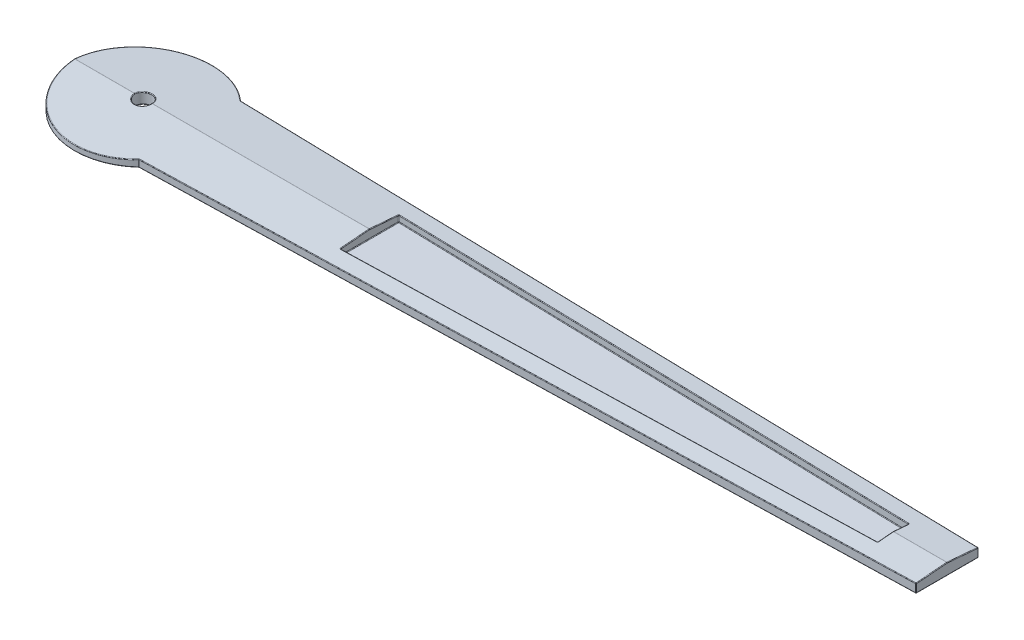
SolidWorks part; units mm, degrees
ref_plane "Front Plane" through (0, 0, 0) normal (0, 0, 1) x (1, 0, 0)
ref_plane "Top Plane" through (0, 0, 0) normal (0, 1, 0) x (1, 0, 0)
ref_plane "Right Plane" through (0, 0, 0) normal (1, 0, 0) x (0, 0, -1)
sketch "Sketch1" plane through (0, 0, 0) normal (0, 1, 0) x (1, 0, 0)
  line L0 (14.2005, 0.633) -> (0.8775, 0.8412)
  line L1 (14.2073, -0.475) -> (0.7499, -0.9567)
  line L2 (14.2005, 0.633) -> (14.2073, -0.475)
  line L3 (13.2032, 0.373) -> (13.1824, -0.2227)
  line L4 (13.1824, -0.2227) -> (3.9608, -0.5357)
  line L5 (3.9608, -0.5357) -> (3.9347, 0.4217)
  line L6 (3.9347, 0.4217) -> (13.2032, 0.373)
  arc A0 (0.8775, 0.8412) -> (0.7499, -0.9567) centre (0, 0) ccw
  circle A1 centre (0, 0) radius 0.15
sketch "Sketch2" plane through (0, 0, 0) normal (0, 1, 0) x (1, 0, 0)
  line L0 (13.25, 0.2746) -> (4, 0.5144)
  line L1 (14.2005, 0.633) -> (14.2073, -0.475) construction
  line L2 (-8.4826, 0) -> (8.4826, 0) construction
  line L3 (14.2044, 0) -> (14.2044, -0.55)
  line L4 (14.2044, 0) -> (14.2044, 0.55)
  line L7 (14.2044, 0.55) -> (0.8206, 0.8969)
  line L8 (0.8206, -0.8969) -> (14.2044, -0.55)
  line L9 (4, -0.5144) -> (13.25, -0.2746)
  line L10 (13.25, 0.2746) -> (13.25, -0.2746)
  line L13 (4, 0.5144) -> (4, -0.5144)
  line L14 (14.1966, 0.2501) -> (0.8128, 0.597) construction
  line L15 (0.8128, -0.597) -> (14.1966, -0.2501) construction
  arc A0 (0.8206, 0.8969) -> (0.8206, -0.8969) centre (0, 0) ccw
  circle A1 centre (0, 0) radius 0.15
  dimension "D1" = 0.55
  dimension "D2" = 0.55
  dimension "D3" = 0.3
  dimension "D4" = 0.3
extrude "Boss-Extrude1" add sketch "Sketch2" along normal blind 0.2
ref_plane "Plane1" through (4, 0, 0.5144) normal (0, 0, 1) x (1, 0, 0)
sketch "Sketch4" plane through (0, 0, 0) normal (0, -1, 0) x (1, 0, 0)
  line L0 (4, -0.5144) -> (4, 0.5144) construction
  line L1 (13.25, -0.2746) -> (4, -0.5144) construction
  line L2 (4, 0.5144) -> (13.25, 0.2746) construction
  line L3 (13.25, 0.2746) -> (13.25, -0.2746) construction
  line L4 (4, -0.5144) -> (4, 0.5144)
  line L5 (13.25, -0.2746) -> (4, -0.5144)
  line L6 (4, 0.5144) -> (13.25, 0.2746)
  line L7 (13.25, 0.2746) -> (13.25, -0.2746)
extrude "Boss-Extrude2" add sketch "Sketch4" against normal blind 0.05
sketch "Sketch5" plane through (0, 0, 0) normal (1, 0, 0) x (0, 0, -1)
  line L0 (-1.2156, 0.1) -> (0, 0.2)
  line L1 (-1.2156, 0.2) -> (-1.2156, 0) construction
  line L2 (-0.55, 0.2) -> (0.55, 0.2) construction
  line L3 (0, 0.2) -> (1.2156, 0.1)
  line L4 (1.2156, 0) -> (1.2156, 0.2) construction
  line L5 (1.2156, 0.1) -> (1.4886, 0.4659)
  line L6 (1.4886, 0.4659) -> (-1.5343, 0.5644)
  line L7 (-1.5343, 0.5644) -> (-1.2156, 0.1)
extrude "Cut-Extrude1" cut sketch "Sketch5" against normal mid plane 40.05
fillet "Fillet1" radius 0.01 34 edges at (4, 0.1788, -0.2572) (8.625, 0.1675, 0.3945) (0.8206, 0.0631, 0.8969) (14.2044, 0.0774, 0.55) (14.2044, 0.0774, -0.55) (0.8206, 0.0631, -0.8969) (7.5125, 0, -0.7234) (14.2044, 0, 0) (7.5125, 0, 0.7234) (-1.2156, 0, 0) (0, 0, 0.15) (13.25, 0.1137, -0.2746) (4, 0.1038, -0.5144) (4, 0.1038, 0.5144) (13.25, 0.1137, 0.2746) (4, 0.05, 0) (8.625, 0.05, 0.3945) (13.25, 0.05, 0) (8.625, 0.05, -0.3945) (-0.49, 0.1085, -1.1125) (14.2044, 0.1774, -0.275) (7.5125, 0.1405, -0.7234) (0, 0.1877, -0.15) (13.25, 0.1887, -0.1373) (8.625, 0.1675, -0.3945) (-0.49, 0.1085, 1.1125) (7.5125, 0.1405, 0.7234) (14.2044, 0.1774, 0.275) (0, 0.1877, 0.15) (13.25, 0.1887, 0.1373) (4, 0.1788, 0.2572) (-0.6828, 0.2, 0) (2.075, 0.2, 0) (13.7272, 0.2, 0)
